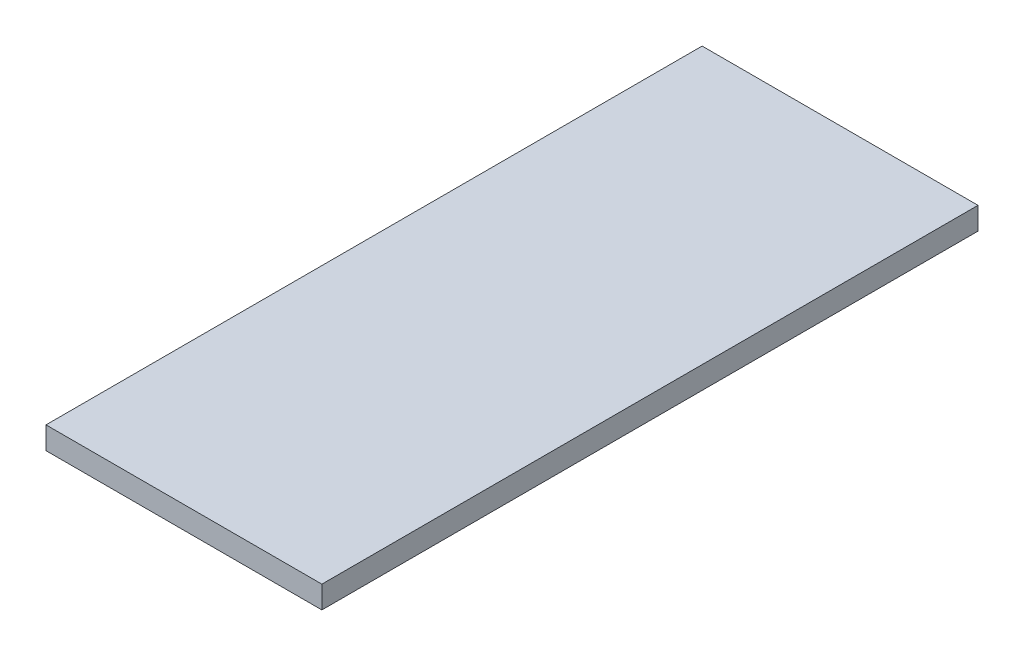
SolidWorks part; units mm, degrees
ref_plane "Front Plane" through (0, 0, 0) normal (0, 0, 1) x (1, 0, 0)
ref_plane "Top Plane" through (0, 0, 0) normal (0, 1, 0) x (1, 0, 0)
ref_plane "Right Plane" through (0, 0, 0) normal (1, 0, 0) x (0, 0, -1)
sketch "Sketch1" plane through (0, 0, 0) normal (0, 1, 0) x (1, 0, 0)
  line L1 (0, 88) -> (37, 88)
  line L2 (0, 88) -> (0, 0)
  line L3 (0, 0) -> (37, 0)
  line L4 (37, 88) -> (37, 0)
extrude "Boss-Extrude1" add sketch "Sketch1" along normal blind 3
